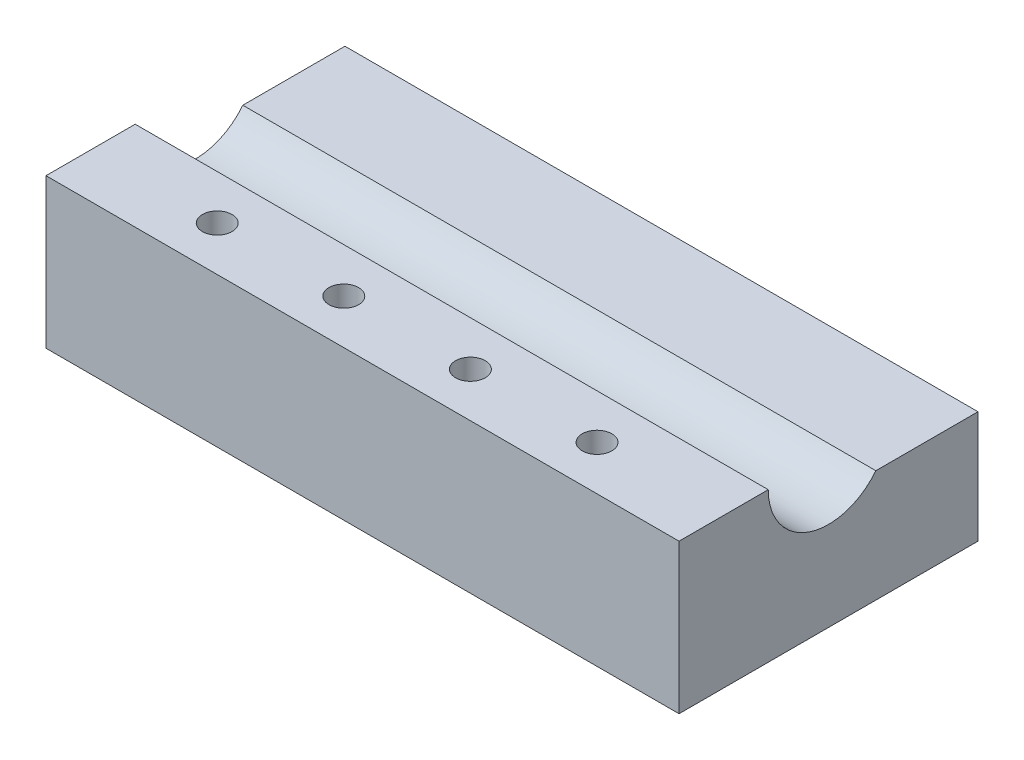
SolidWorks part; units mm, degrees
ref_plane "Front Plane" through (0, 0, 0) normal (0, 0, 1) x (1, 0, 0)
ref_plane "Top Plane" through (0, 0, 0) normal (0, 1, 0) x (1, 0, 0)
ref_plane "Right Plane" through (0, 0, 0) normal (1, 0, 0) x (0, 0, -1)
sketch "Sketch1" plane through (0, 0, 0) normal (0, 1, 0) x (1, 0, 0)
  line L1 (0, 0) -> (25.41, 0)
  line L2 (0, 0) -> (0, 12)
  line L3 (0, 12) -> (25.41, 12)
  line L4 (25.41, 0) -> (25.41, 12)
extrude "Boss-Extrude1" add sketch "Sketch1" along normal blind 6 contours L3 L4 L1 L2
sketch "Sketch2" plane through (0, 0, 0) normal (-1, 0, 0) x (0, 0, 1)
  line L0 (0, 6) -> (-12, 6) construction
  circle A0 centre (-6, 6) radius 2.42
extrude "Cut-Extrude1" cut sketch "Sketch2" against normal blind 25.41
sketch "Sketch4" plane through (0, 0, 0) normal (-1, 0, 0) x (0, 0, 1)
  line L1 (-12, 6) -> (-7.4776, 6)
  line L2 (-12, 6) -> (-12, 4.5)
  line L3 (-12, 4.5) -> (-7.4776, 4.5)
  line L4 (-7.4776, 6) -> (-7.4776, 4.5)
extrude "Cut-Extrude2" cut sketch "Sketch4" against normal blind 25.41
sketch "Sketch5" plane through (0, 0, 0) normal (0, -1, 0) x (-1, 0, 0)
  line L6 (-1.5, 6) -> (0, 6)
  line L7 (0, 0) -> (0, 12) construction
  line L8 (-23.91, 6) -> (-25.41, 6)
  line L9 (-25.41, 0) -> (-25.41, 12) construction
hole_wizard "#2-56 Tapped Hole1" positions "Sketch8" profile "Sketch9" tap size "#2-56" standard "ANSI Inch"
sketch "Sketch8" plane through (0, 0, 0) normal (0, -1, 0) x (-1, 0, 0)
  point P0 (-23.91, 6)
  point P3 (-1.5, 6)
sketch "Sketch9" plane through (23.91, 0, -6) normal (1, 0, 0) x (0, 0, -1)
  line L0 (0, 0) -> (0, 3.25)
  line L1 (0, 3.25) -> (1, 2.6491)
  line L2 (1, 2.6491) -> (1, 0)
  line L5 (1, 0) -> (0, 0)
  line L10 (0, 3.25) -> (-1, 2.6491) construction
  line L11 (0, -6.35) -> (0, 107.95) construction
  dimension "Tap Drill Dia." = 2
  dimension "Tap Drill Depth" = 3.25
  dimension "Drill Angle" = 118
sketch "Sketch10" plane through (0, 6, 0) normal (0, 1, 0) x (1, 0, 0)
  line L0 (0, 1.79) -> (25.41, 1.79)
  line L1 (0, 0) -> (0, 3.58) construction
  line L2 (25.41, 0) -> (25.41, 3.58) construction
  line L3 (0, 1.79) -> (5.082, 1.79)
  line L4 (5.082, 1.79) -> (10.164, 1.79)
  line L5 (10.164, 1.79) -> (15.246, 1.79)
  line L6 (15.246, 1.79) -> (20.328, 1.79)
hole_wizard "#0-80 Tapped Hole1" positions "Sketch11" profile "Sketch12" tap size "#0-80" standard "ANSI Inch"
sketch "Sketch11" plane through (0, 6, 0) normal (0, 1, 0) x (1, 0, 0)
  point P0 (5.082, 1.79)
  point P3 (10.164, 1.79)
  point P6 (15.246, 1.79)
  point P9 (20.328, 1.79)
sketch "Sketch12" plane through (5.082, 6, -1.79) normal (1, 0, 0) x (0, 0, 1)
  line L0 (0, 0) -> (0, 4)
  line L1 (0, 4) -> (0.5956, 3.6421)
  line L2 (0.5956, 3.6421) -> (0.5956, 0)
  line L5 (0.5956, 0) -> (0, 0)
  line L10 (0, 4) -> (-0.5956, 3.6421) construction
  line L11 (0, -6.35) -> (0, 107.95) construction
  dimension "Tap Drill Dia." = 1.1913
  dimension "Tap Drill Depth" = 4
  dimension "Drill Angle" = 118
